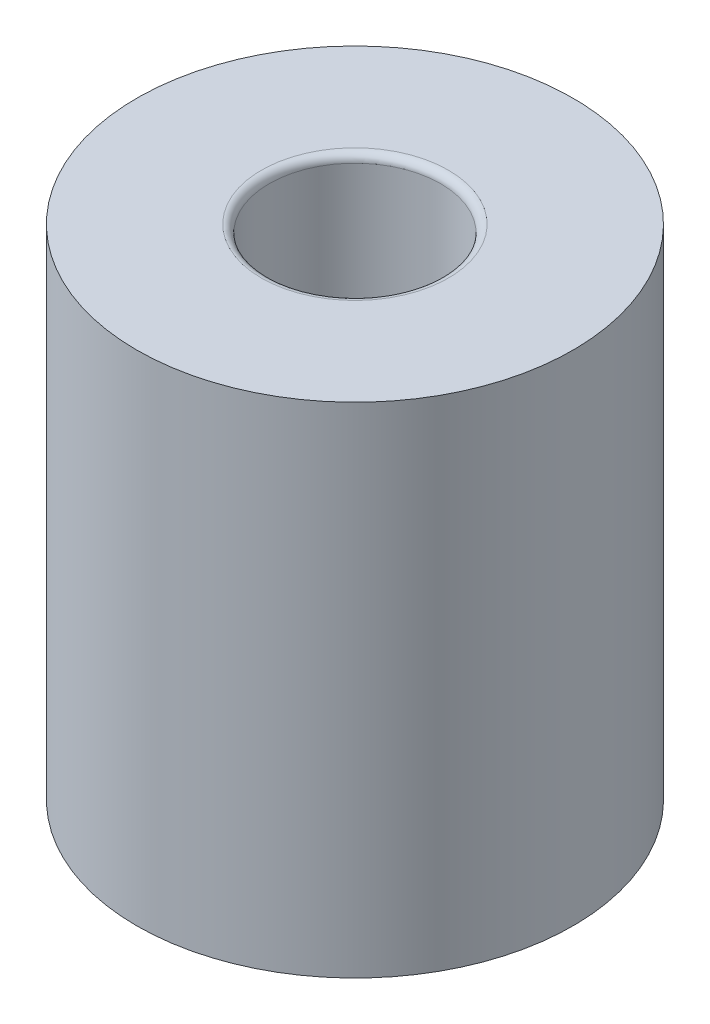
SolidWorks part; units mm, degrees
ref_plane "Front Plane" through (0, 0, 0) normal (0, 0, 1) x (1, 0, 0)
ref_plane "Top Plane" through (0, 0, 0) normal (0, 1, 0) x (1, 0, 0)
ref_plane "Right Plane" through (0, 0, 0) normal (1, 0, 0) x (0, 0, -1)
sketch "Sketch1" plane through (0, 0, 0) normal (0, 1, 0) x (1, 0, 0)
  circle A0 centre (0, 0) radius 3.5
  dimension "D1" = 7
extrude "Boss-Extrude1" add sketch "Sketch1" along normal blind 8
sketch "Sketch2" plane through (0, 8, 0) normal (0, 1, 0) x (1, 0, 0)
  circle A0 centre (0, 0) radius 1.375
  dimension "D1" = 2.75
extrude "Cut-Extrude1" cut sketch "Sketch2" against normal blind 8
fillet "Fillet1" radius 0.125 2 edges at (0, 0, 1.375) (0, 8, 1.375)
